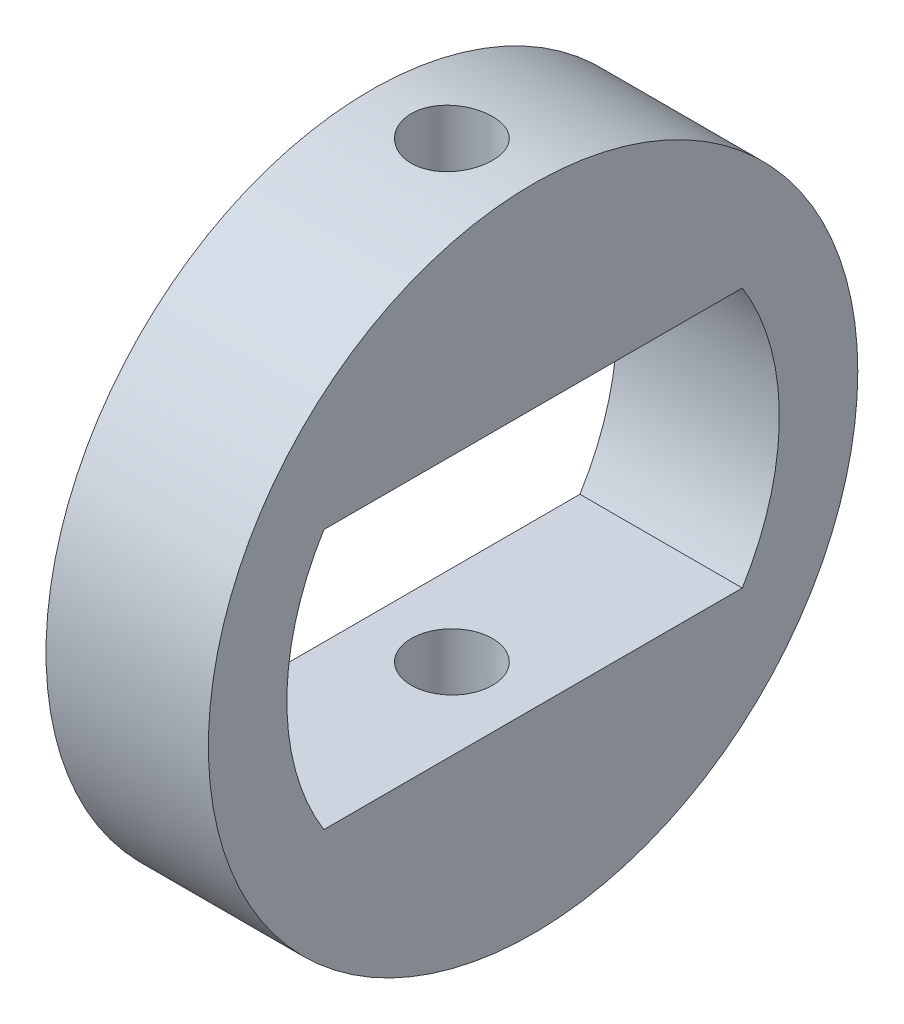
SolidWorks part; units mm, degrees
ref_plane "Front Plane" through (0, 0, 0) normal (0, 0, 1) x (1, 0, 0)
ref_plane "Top Plane" through (0, 0, 0) normal (0, 1, 0) x (1, 0, 0)
ref_plane "Right Plane" through (0, 0, 0) normal (1, 0, 0) x (0, 0, -1)
sketch "Sketch1" plane through (0, 0, 0) normal (1, 0, 0) x (0, 0, -1)
  line L0 (-3.8656, 2.4) -> (3.8656, 2.4)
  line L1 (-3.8656, -2.4) -> (3.8656, -2.4)
  line L2 (-3.7239, 2.15) -> (3.7239, 2.15) construction
  line L3 (-3.7239, -2.15) -> (3.7239, -2.15) construction
  circle A0 centre (0, 0) radius 6
  arc A1 (3.8656, 2.4) -> (3.8656, -2.4) centre (0, 0) cw
  arc A2 (-3.8656, 2.4) -> (-3.8656, -2.4) centre (0, 0) ccw
  arc A3 (3.7239, 2.15) -> (3.7239, -2.15) centre (0, 0) cw construction
  arc A4 (-3.7239, 2.15) -> (-3.7239, -2.15) centre (0, 0) ccw construction
  dimension "D1" = 0.25
extrude "Boss-Extrude1" add sketch "Sketch1" along normal blind 3
sketch "Sketch2" plane through (0, -2.4, 0) normal (0, 1, 0) x (1, 0, 0)
  line L0 (0, 0) -> (3, 0) construction
  line L1 (3, -6) -> (3, 6) construction
  circle A0 centre (1.5, 0) radius 0.75
  dimension "D1" = 1.5
extrude "Cut-Extrude1" cut sketch "Sketch2" against normal through all both and the other way through all
